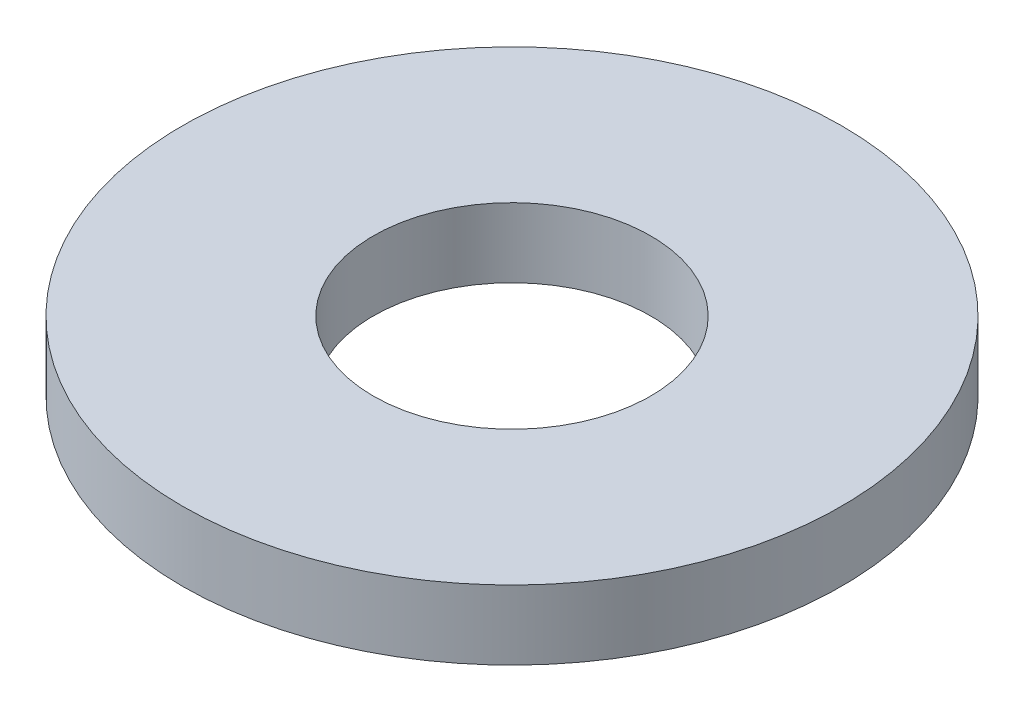
SolidWorks part; units mm, degrees
ref_plane "Front Plane" through (0, 0, 0) normal (0, 0, 1) x (1, 0, 0)
ref_plane "Top Plane" through (0, 0, 0) normal (0, 1, 0) x (1, 0, 0)
ref_plane "Right Plane" through (0, 0, 0) normal (1, 0, 0) x (0, 0, -1)
sketch "Sketch1" plane through (0, 0, 0) normal (0, 1, 0) x (1, 0, 0)
  circle A0 centre (0, 0) radius 9.5
  circle A1 centre (0, 0) radius 4
  dimension "D1" = 8
  dimension "D2" = 19
extrude "Boss-Extrude1" add sketch "Sketch1" along normal blind 2
